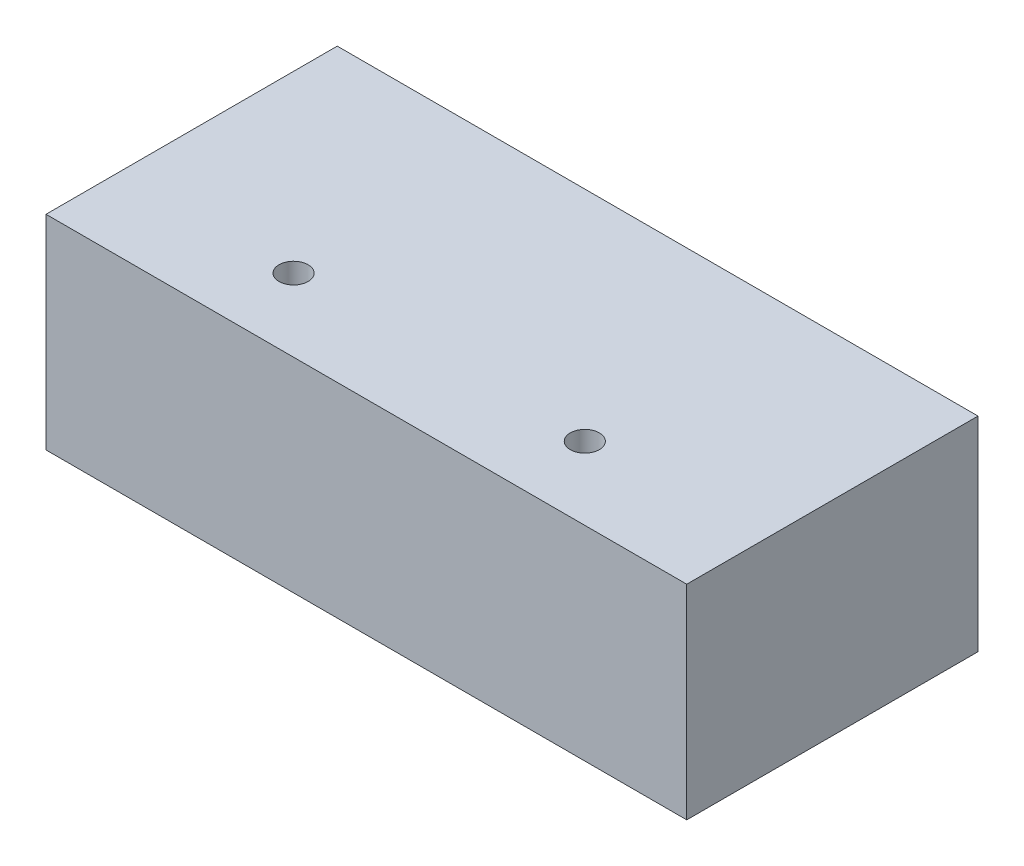
SolidWorks part; units mm, degrees
ref_plane "Alzado" through (0, 0, 0) normal (0, 0, 1) x (1, 0, 0)
ref_plane "Planta" through (0, 0, 0) normal (0, 1, 0) x (1, 0, 0)
ref_plane "Vista lateral" through (0, 0, 0) normal (1, 0, 0) x (0, 0, -1)
sketch "Croquis1" plane through (0, 0, 0) normal (0, 0, 1) x (1, 0, 0)
  line L1 (-26.4, -8.41) -> (26.4, -8.41)
  line L2 (-26.4, -8.41) -> (-26.4, 8.41)
  line L3 (-26.4, 8.41) -> (26.4, 8.41)
  line L4 (26.4, -8.41) -> (26.4, 8.41)
  line L5 (-26.4, -8.41) -> (26.4, 8.41) construction
  line L6 (-26.4, 8.41) -> (26.4, -8.41) construction
  point P0 (0, 0)
extrude "Saliente-Extruir1" add sketch "Croquis1" along normal blind 30
sketch "Croquis2" plane through (0, 8.41, 0) normal (0, 1, 0) x (1, 0, 0)
  line L1 (26.4, -30) -> (-26.4, -30) construction
  line L10 (12, -42) -> (-12, -18) construction
  line L11 (12, -18) -> (-12, -42) construction
  circle A1 centre (-12, -18) radius 1.2
  circle A2 centre (12, -18) radius 1.2
  point P2 (0, -30)
extrude "Cortar-Extruir1" cut sketch "Croquis2" against normal blind 20
sketch "Croquis3" plane through (0, 0, 0) normal (0, 0, 1) x (1, 0, 0)
  circle A6 centre (18.6, 0) radius 1.2
  circle A7 centre (7, 0) radius 1.2
  circle A8 centre (-7, 0) radius 1.2
  circle A9 centre (-18.6, 0) radius 1.2
extrude "Cortar-Extruir2" cut sketch "Croquis3" along normal blind 10
sketch "Croquis4" plane through (0, 0, 30) normal (0, 0, 1) x (1, 0, 0)
  line L1 (-26.4, -8.41) -> (26.4, -8.41)
  line L2 (-26.4, -8.41) -> (-26.4, 8.41)
  line L3 (-26.4, 8.41) -> (26.4, 8.41)
  line L4 (26.4, -8.41) -> (26.4, 8.41)
extrude "Cortar-Extruir3" cut sketch "Croquis4" against normal blind 6
